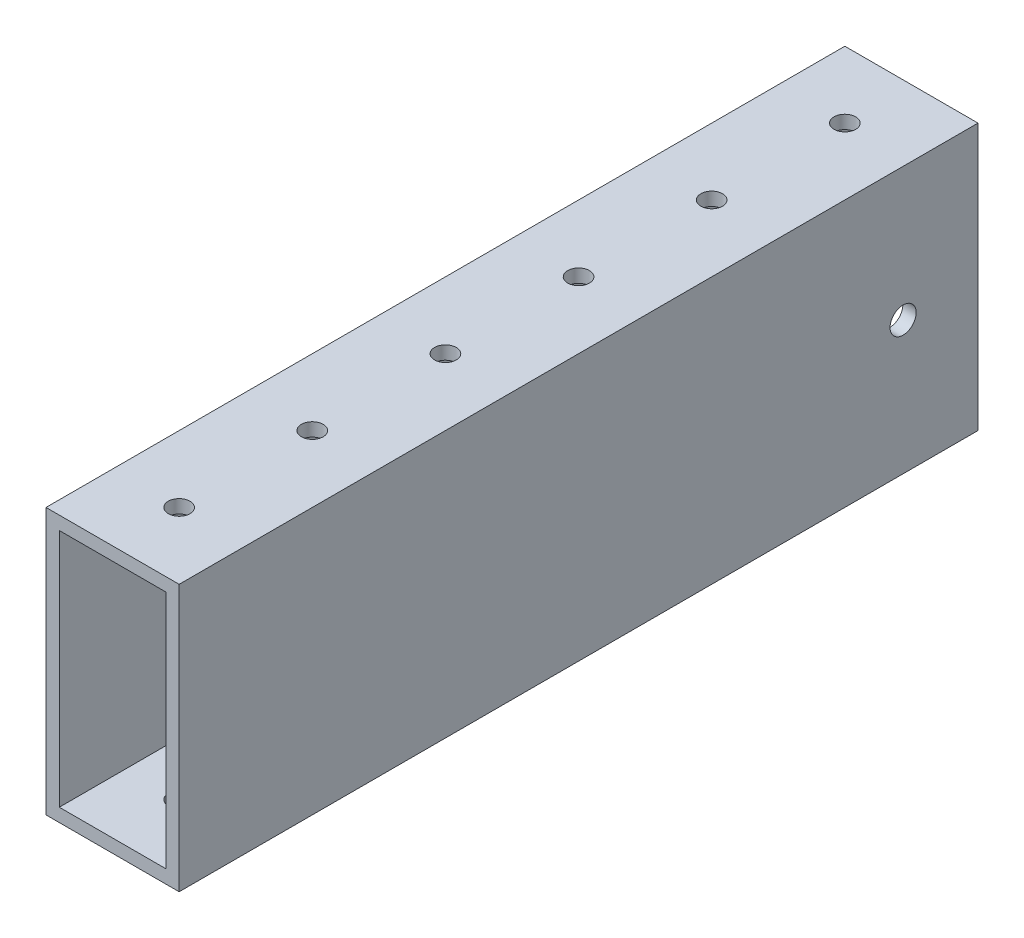
SolidWorks part; units mm, degrees
ref_plane "Front" through (0, 0, 0) normal (0, 0, 1) x (1, 0, 0)
ref_plane "Top" through (0, 0, 0) normal (0, 1, 0) x (1, 0, 0)
ref_plane "Right" through (0, 0, 0) normal (1, 0, 0) x (0, 0, -1)
sketch "Sketch1" plane through (0, 0, 0) normal (0, 0, 1) x (1, 0, 0)
  line L5 (-12.7, -25.4) -> (12.7, -25.4)
  line L6 (-12.7, -25.4) -> (-12.7, 25.4)
  line L7 (-12.7, 25.4) -> (12.7, 25.4)
  line L8 (12.7, -25.4) -> (12.7, 25.4)
  line L9 (-12.7, -25.4) -> (12.7, 25.4) construction
  line L10 (-12.7, 25.4) -> (12.7, -25.4) construction
  point P0 (0, 0)
  dimension "D1" = 50.8
  dimension "D2" = 25.4
extrude "Extrude-Thin1" add sketch "Sketch1" along normal mid plane 152.4 thin thin type one direction reverse wall 2.54
sketch "Sketch2" plane through (0, 25.4, 0) normal (0, 1, 0) x (1, 0, 0)
  line L0 (0, -76.2) -> (0, -63.5) construction
  line L1 (12.7, -76.2) -> (-12.7, -76.2) construction
  circle A0 centre (0, -63.5) radius 2.0701
  dimension "D1" = 4.1402
  dimension "D2" = 12.7
extrude "Cut-Extrude1" cut sketch "Sketch2" against normal through all
pattern_linear "LPattern1" count 7 spacing 25.4 along (0, 0, -1) of "Cut-Extrude1"
sketch "Sketch3" plane through (12.7, 0, 0) normal (1, 0, 0) x (0, 0, -1)
  line L0 (76.2, 0) -> (61.9125, 0) construction
  line L1 (76.2, -25.4) -> (76.2, 25.4) construction
  circle A0 centre (61.9125, 0) radius 2.4892
  dimension "D2" = 4.9784
  dimension "D1" = 14.2875
extrude "Cut-Extrude2" cut sketch "Sketch3" against normal through all
equation "\"lenght\"= 6"
equation "\"D1@Extrude-Thin1\"=\"lenght\""
equation "\"D1@LPattern1\"=\"lenght\"+1"
